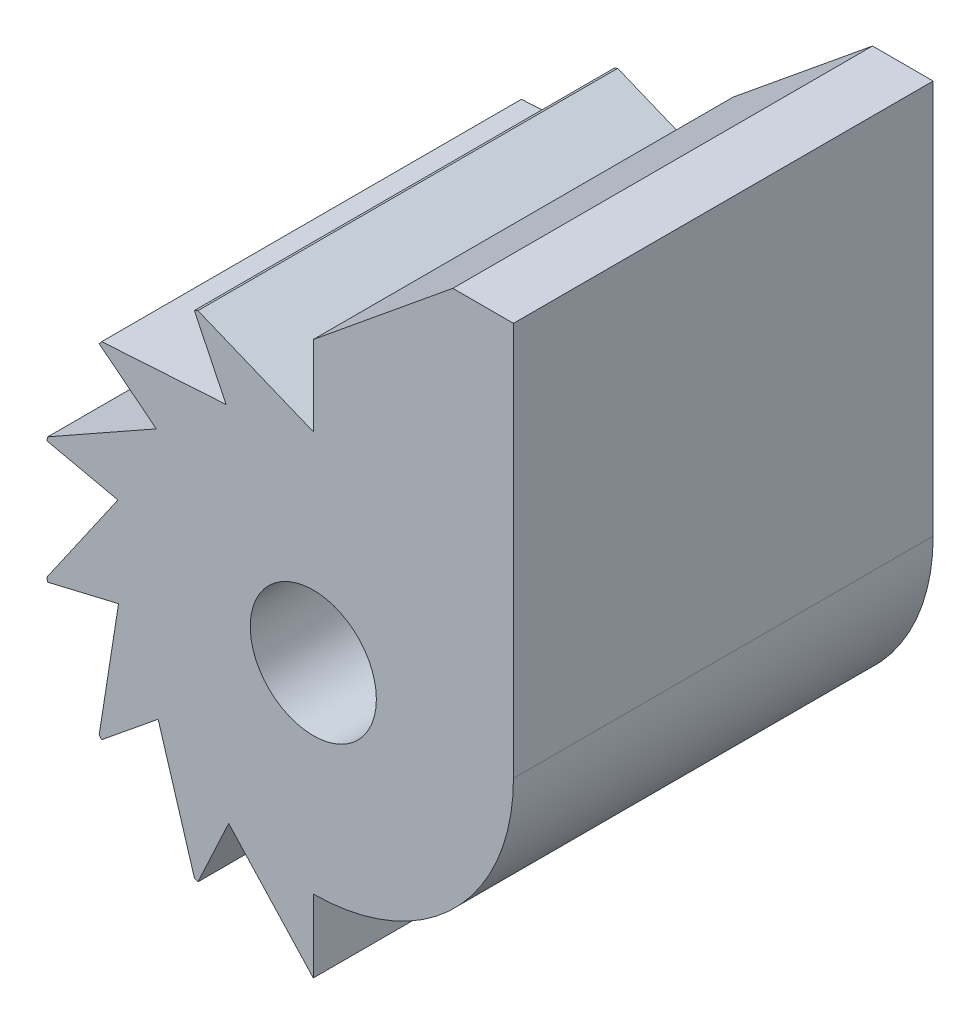
SolidWorks part; units mm, degrees
material "ABS"
ref_plane "Front Plane" through (0, 0, 0) normal (0, 0, 1) x (1, 0, 0)
ref_plane "Top Plane" through (0, 0, 0) normal (0, 1, 0) x (1, 0, 0)
ref_plane "Right Plane" through (0, 0, 0) normal (1, 0, 0) x (0, 0, -1)
sketch "Sketch1" plane through (0, 0, 0) normal (0, 0, 1) x (1, 0, 0)
  line L0 (10.4775, 0) -> (10.4775, 14.28)
  line L1 (7.3025, 14.28) -> (7.3025, 20.63)
  line L2 (-0.4637, 14.28) -> (7.3025, 14.28)
  line L3 (7.3025, 20.63) -> (10.4775, 20.63)
  line L4 (0, 0) -> (-10.4775, 0) construction
  line L5 (-10.4775, 0) -> (-14.2875, 0)
  line L7 (0, 0) -> (-0.3401, 10.472) construction
  line L8 (-0.3401, 10.472) -> (-0.4637, 14.28)
  line L9 (0, 0) -> (0, -10.4775) construction
  line L10 (0, -10.4775) -> (0, -14.2875)
  line L11 (10.4775, 20.63) -> (10.4775, 14.28)
  line L12 (7.3025, 14.28) -> (10.4775, 14.28) construction
  line L13 (7.3025, 20.63) -> (-0.4637, 14.28)
  circle A0 centre (0, 0) radius 10.4775
  circle A1 centre (0, 0) radius 3.302
  arc A2 (-14.2875, 0) -> (-0.4637, 14.28) centre (0, 0) cw
  circle A3 centre (0, 0) radius 14.2875 construction
  arc A8 (0, -14.2875) -> (-14.2875, 0) centre (0, 0) cw
  dimension "D1" = 6.604
  dimension "D2" = 28.575
  dimension "D5" = 88.14
  dimension "D3" = 6.35
  dimension "D4" = 3.175
  dimension "D6" = 3.81
extrude "Boss-Extrude1" add sketch "Sketch1" along normal blind 21.971
sketch "Sketch3" plane through (0, 0, 21.971) normal (0, 0, 1) x (1, 0, 0)
  line L0 (0, 0) -> (0, -10.4775) construction
  line L1 (0, -10.4775) -> (0, -14.2875) construction
  line L2 (0, -10.4775) -> (0, -14.2875) construction
  line L3 (0, -14.2875) -> (-4.428, -9.4958)
  line L4 (-4.428, -9.4958) -> (0, 0) construction
  line L5 (-4.428, -9.4958) -> (-6.0382, -12.9489)
  line L6 (-8.1233, -6.6174) -> (-11.0773, -9.0237)
  line L7 (-6.2258, -12.8597) -> (-8.1233, -6.6174)
  line L8 (-10.1951, -2.4163) -> (-13.9024, -3.2949)
  line L9 (-11.2073, -8.8616) -> (-10.1951, -2.4163)
  line L10 (-10.2291, 2.2677) -> (-13.9488, 3.0924)
  line L11 (-13.9488, -3.0924) -> (-10.2291, 2.2677)
  line L12 (-8.2187, 6.4985) -> (-11.2073, 8.8616)
  line L13 (-13.9024, 3.2949) -> (-8.2187, 6.4985)
  line L14 (-4.5656, 9.4304) -> (-6.2258, 12.8597)
  line L15 (-11.0773, 9.0237) -> (-4.5656, 9.4304)
  line L16 (0, 10.4775) -> (0, 14.2875)
  line L17 (-6.0382, 12.9489) -> (0, 10.4775)
  circle A0 centre (0, 0) radius 10.4775 construction
  circle A1 centre (0, 0) radius 14.2875 construction
  arc A2 (0, -10.4775) -> (-4.428, -9.4958) centre (0, 0) cw construction
  arc A3 (0, -14.2875) -> (-6.0382, -12.9489) centre (0, 0) cw
  arc A4 (-6.2258, -12.8597) -> (-11.0773, -9.0237) centre (0, 0) cw
  arc A5 (-11.2073, -8.8616) -> (-13.9024, -3.2949) centre (0, 0) cw
  arc A6 (-13.9488, -3.0924) -> (-13.9488, 3.0924) centre (0, 0) cw
  arc A7 (-13.9024, 3.2949) -> (-11.2073, 8.8616) centre (0, 0) cw
  arc A8 (-11.0773, 9.0237) -> (-6.2258, 12.8597) centre (0, 0) cw
  arc A9 (-6.0382, 12.9489) -> (0, 14.2875) centre (0, 0) cw
  point P34 (0, 0)
  dimension "D1" = 25
extrude "Cut-Extrude1" cut sketch "Sketch3" against normal through all
sketch "Sketch4" plane through (0, 0, 21.971) normal (0, 0, 1) x (1, 0, 0)
  line L0 (-0.4637, 14.28) -> (0, 14.2875)
  line L1 (0, 14.2875) -> (0, 14.6591)
  line L2 (7.3025, 20.63) -> (-0.4637, 14.28) construction
  line L3 (0, 14.6591) -> (-0.4637, 14.28)
extrude "Cut-Extrude2" cut sketch "Sketch4" against normal through all
